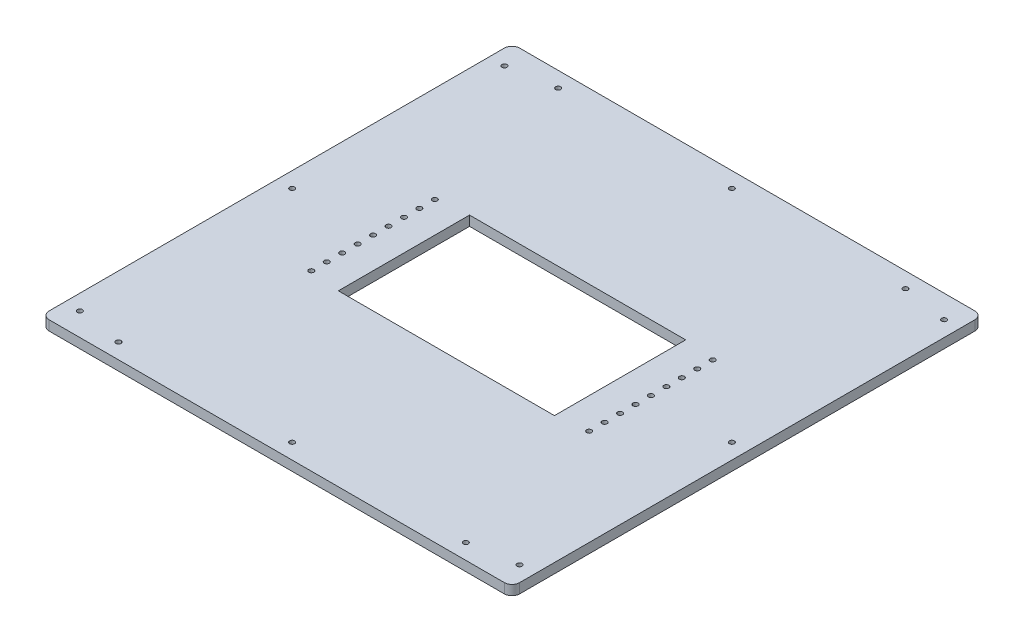
SolidWorks part; units mm, degrees
material "PC High Viscosity"
ref_plane "Front Plane" through (0, 0, 0) normal (0, 0, 1) x (1, 0, 0)
ref_plane "Top Plane" through (0, 0, 0) normal (0, 1, 0) x (1, 0, 0)
ref_plane "Right Plane" through (0, 0, 0) normal (1, 0, 0) x (0, 0, -1)
sketch "Sketch1" plane through (0, 0, 0) normal (0, 1, 0) x (1, 0, 0)
  line L1 (-304.8, 304.8) -> (304.8, 304.8)
  line L2 (-304.8, 304.8) -> (-304.8, -304.8)
  line L3 (-304.8, -304.8) -> (304.8, -304.8)
  line L4 (304.8, 304.8) -> (304.8, -304.8)
  line L5 (-304.8, 304.8) -> (304.8, -304.8) construction
  line L6 (-304.8, -304.8) -> (304.8, 304.8) construction
  point P0 (0, 0)
  dimension "D1" = 609.6
extrude " Lexan Boss-Extrude1" add sketch "Sketch1" along normal blind 12.7
sketch "Sketch5" plane through (0, 0, 0) normal (0, -1, 0) x (1, 0, 0)
  line L1 (-140, 85) -> (140, 85)
  line L2 (-140, 85) -> (-140, -85)
  line L3 (-140, -85) -> (140, -85)
  line L4 (140, 85) -> (140, -85)
  line L5 (-140, 85) -> (140, -85) construction
  line L6 (-140, -85) -> (140, 85) construction
  line L7 (-115, 55) -> (115, 55) construction
  line L8 (-115, 55) -> (-115, -55) construction
  line L9 (-115, -55) -> (115, -55) construction
  line L10 (115, 55) -> (115, -55) construction
  line L11 (-115, 55) -> (115, -55) construction
  line L12 (-115, -55) -> (115, 55) construction
  point P0 (0, 0)
  point P6 (0, 0)
  dimension "D1" = 280
  dimension "D2" = 170
  dimension "D3" = 230
  dimension "D4" = 110
extrude "Housing nest hole Cut-Extrude1" cut sketch "Sketch5" against normal up to next
sketch "Sketch6" plane through (0, 0, 0) normal (0, -1, 0) x (1, 0, 0)
  line L0 (-284.8, 275) -> (-284.8, -275) construction
  line L1 (-284.8, 0) -> (0, 0) construction
  line L2 (-304.8, -304.8) -> (-304.8, 304.8) construction
  line L3 (0, 0) -> (0, 304.8) construction
  line L4 (-304.8, 304.8) -> (304.8, 304.8) construction
  line L5 (-225, 284.8) -> (225, 284.8) construction
  circle A0 centre (-284.8, 275) radius 3.25
  circle A1 centre (-284.8, 0) radius 3.25
  circle A2 centre (-284.8, -275) radius 3.25
  circle A3 centre (284.8, -275) radius 3.25
  circle A4 centre (284.8, 0) radius 3.25
  circle A5 centre (284.8, 275) radius 3.25
  circle A6 centre (-225, 284.8) radius 3.25
  circle A7 centre (0, 284.8) radius 3.25
  circle A8 centre (225, 284.8) radius 3.25
  circle A9 centre (225, -284.8) radius 3.25
  circle A10 centre (0, -284.8) radius 3.25
  circle A11 centre (-225, -284.8) radius 3.25
  dimension "D3" = 6.5
  dimension "D1" = 550
  dimension "D2" = 20
  dimension "D4" = 20
  dimension "D5" = 450
extrude "Cut-Extrude7" cut sketch "Sketch6" against normal up to next
sketch "Sketch9" plane through (0, 12.7, 0) normal (0, 1, 0) x (1, 0, 0)
  line L0 (0, 0) -> (0, 179.44) construction
  line L1 (0, 0) -> (-180, 0) construction
  line L2 (0, 0) -> (180, 0) construction
  circle A0 centre (-180, 0) radius 3.25
  circle A1 centre (180, 0) radius 3.25
  dimension "D1" = 6.5
  dimension "D2" = 180
extrude "Cut-Extrude6" cut sketch "Sketch9" against normal through all
pattern_linear "LPattern5" count 5 spacing 20 along (0, 0, 1) count 5 spacing 20 along (0, 0, -1) of "Cut-Extrude6"
fillet "Fillet3" radius 10 4 edges at (-304.8, 6.35, -304.8) (304.8, 6.35, -304.8) (304.8, 6.35, 304.8) (-304.8, 6.35, 304.8)
